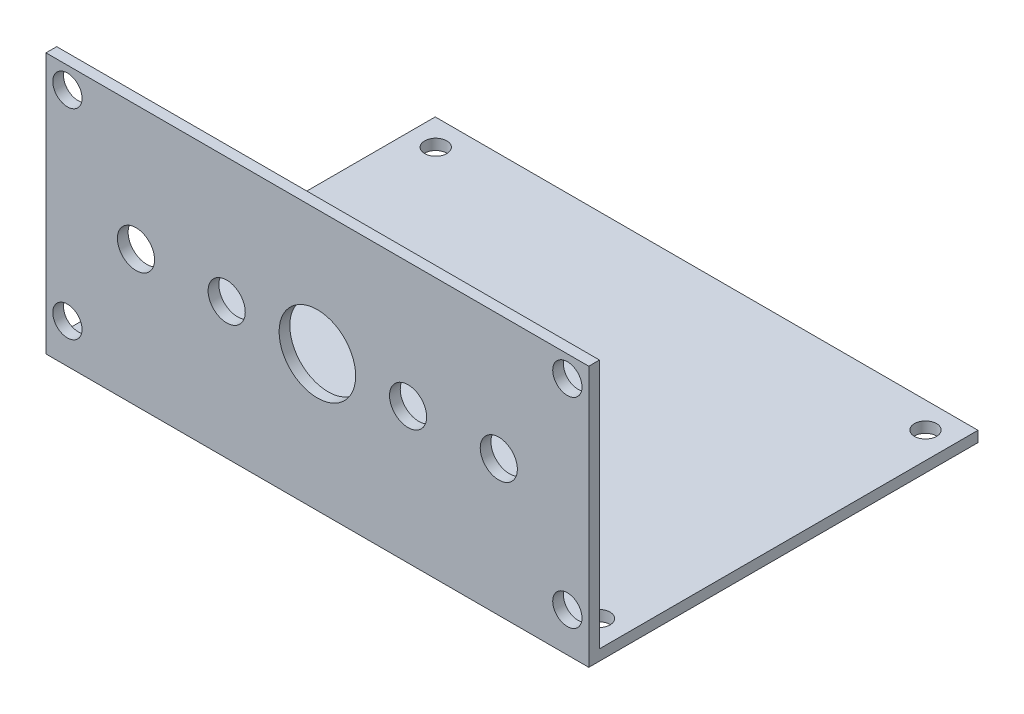
SolidWorks part; units mm, degrees
material "PTFE(普通)"
ref_plane "前视基准面" through (0, 0, 0) normal (0, 0, 1) x (1, 0, 0)
ref_plane "上视基准面" through (0, 0, 0) normal (0, 1, 0) x (1, 0, 0)
ref_plane "右视基准面" through (0, 0, 0) normal (1, 0, 0) x (0, 0, -1)
other "Configuration Table"
sketch "草图1" plane through (0, 0, 0) normal (0, 1, 0) x (1, 0, 0)
  line L1 (34.29, -22.86) -> (-34.29, -22.86) construction
  line L2 (34.29, -22.86) -> (34.29, 22.86) construction
  line L3 (34.29, 22.86) -> (-34.29, 22.86) construction
  line L4 (-34.29, -22.86) -> (-34.29, 22.86) construction
  line L5 (34.29, -22.86) -> (-34.29, 22.86) construction
  line L6 (34.29, 22.86) -> (-34.29, -22.86) construction
  line L7 (38, -26.5) -> (-38, -26.5)
  line L8 (38, -26.5) -> (38, 26.5)
  line L9 (38, 26.5) -> (-38, 26.5)
  line L10 (-38, -26.5) -> (-38, 26.5)
  line L11 (38, -26.5) -> (-38, 26.5) construction
  line L12 (38, 26.5) -> (-38, -26.5) construction
  circle A0 centre (-34.29, 22.86) radius 1.55
  circle A1 centre (-34.29, -22.86) radius 1.55
  circle A2 centre (34.29, -22.86) radius 1.55
  circle A3 centre (34.29, 22.86) radius 1.55
  point P0 (0, 0)
  point P10 (0, 0)
  dimension "D3" = 3.1
  dimension "D4" = 3.1
  dimension "D5" = 3.1
  dimension "D6" = 3.1
  dimension "D1" = 22.86
  dimension "D2" = 34.29
  dimension "D7" = 38
  dimension "D8" = 26.5
extrude "凸台-拉伸1" add sketch "草图1" along normal blind 1.5
sketch "草图2" plane through (0, 0, 26.5) normal (0, 0, 1) x (1, 0, 0)
  line L1 (-38, 1.5) -> (38, 1.5)
  line L2 (-38, 1.5) -> (-38, 0)
  line L3 (-38, 0) -> (38, 0)
  line L4 (38, 1.5) -> (38, 0)
extrude "凸台-拉伸2" add sketch "草图2" along normal blind 1.5 contours L3 L4 L1 L2
sketch "草图3" plane through (0, 1.5, 0) normal (0, 1, 0) x (1, 0, 0)
  line L0 (38, -28) -> (38, 26.5) construction
  line L1 (-38, -28) -> (38, -28)
  line L2 (-38, -28) -> (-38, -26.5)
  line L3 (-38, -26.5) -> (38, -26.5)
  line L4 (38, -28) -> (38, -26.5)
  dimension "D1" = 1.5
extrude "凸台-拉伸3" add sketch "草图3" along normal blind 35.02
sketch "草图4" plane through (0, 0, 26.5) normal (0, 0, -1) x (-1, 0, 0)
  line L0 (-38, 1.5) -> (38, 1.5) construction
  line L1 (-38, 36.52) -> (-38, 1.5) construction
  circle A0 centre (0, 19.02) radius 5.36
  circle A1 centre (-12.7, 19.02) radius 2.6
  circle A2 centre (-25.4, 19.02) radius 2.6
  circle A3 centre (12.7, 19.02) radius 2.6
  circle A4 centre (25.4, 19.02) radius 2.6
  dimension "D2" = 10.72
  dimension "D6" = 5.2
  dimension "D7" = 5.2
  dimension "D10" = 5.2
  dimension "D11" = 5.2
  dimension "D1" = 17.52
  dimension "D3" = 38
  dimension "D4" = 12.7
  dimension "D5" = 12.7
  dimension "D8" = 12.7
  dimension "D9" = 12.7
extrude "切除-拉伸1" cut sketch "草图4" against normal blind 60
sketch "草图5" plane through (0, 0, 26.5) normal (0, 0, -1) x (-1, 0, 0)
  line L0 (-38, 36.52) -> (38, 36.52) construction
  line L2 (-38, 36.52) -> (-38, 1.5) construction
  line L3 (38, 36.52) -> (38, 1.5) construction
  line L4 (-38, 1.5) -> (38, 1.5) construction
  line L5 (-35, 33.52) -> (-35, 5.5) construction
  line L6 (-35, 5.5) -> (35, 5.5) construction
  circle A0 centre (-35, 33.52) radius 2.05
  circle A1 centre (-35, 5.5) radius 2.05
  circle A2 centre (35, 5.5) radius 2.05
  circle A3 centre (35, 33.52) radius 2.05
  dimension "D1" = 4.1
  dimension "D2" = 4.1
  dimension "D3" = 4.1
  dimension "D4" = 4.1
  dimension "D5" = 3
  dimension "D6" = 3
  dimension "D7" = 3
  dimension "D8" = 4
  dimension "D9" = 28.02
  dimension "D10" = 70
extrude "切除-拉伸2" cut sketch "草图5" against normal blind 10
